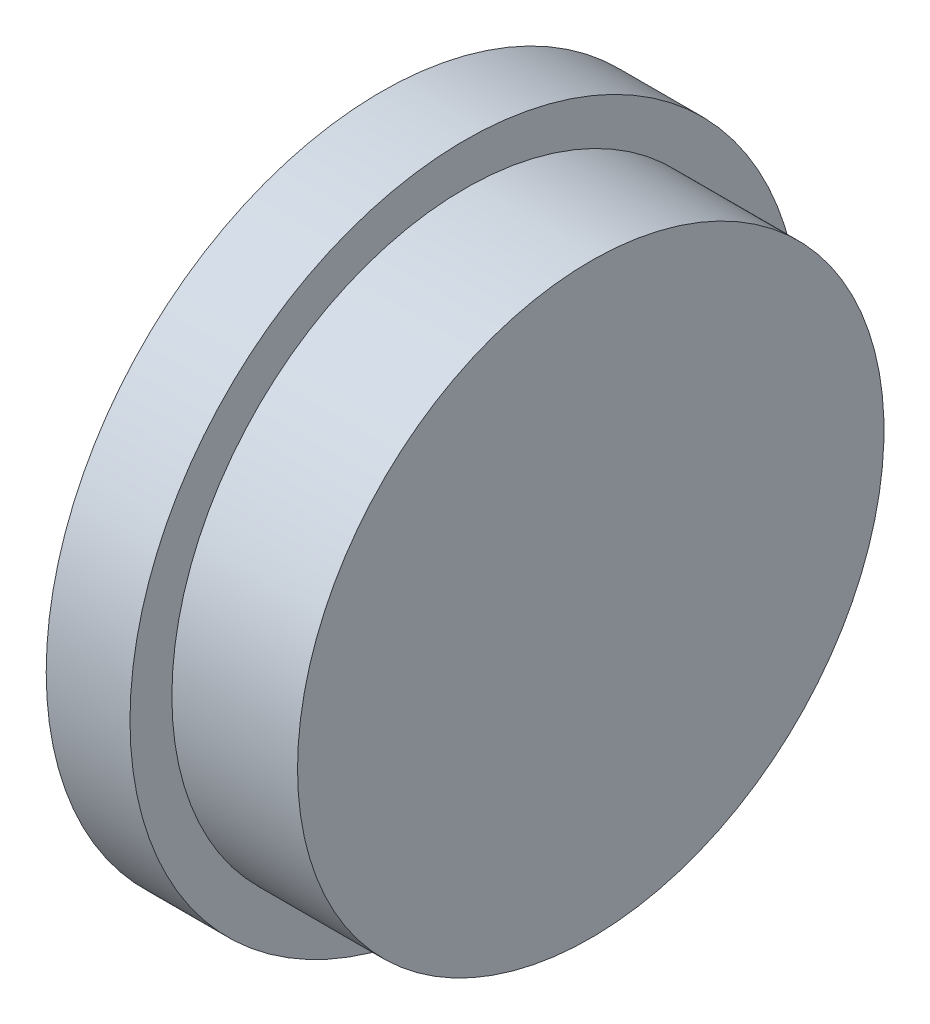
SolidWorks part; units mm, degrees
ref_plane "Plan de face" through (0, 0, 0) normal (0, 0, 1) x (1, 0, 0)
ref_plane "Plan de dessus" through (0, 0, 0) normal (0, 1, 0) x (1, 0, 0)
ref_plane "Plan de droite" through (0, 0, 0) normal (1, 0, 0) x (0, 0, -1)
sketch "Esquisse2" plane through (0, 0, 0) normal (0, 0, 1) x (1, 0, 0)
  line L0 (0, 0) -> (13, 0) construction
  line L1 (13, 0) -> (13, 16)
  line L2 (13, 16) -> (0, 16)
  line L3 (0, 16) -> (0, 24)
  line L4 (0, 24) -> (6, 24)
  line L5 (6, 24) -> (6, 21)
  line L6 (6, 21) -> (15, 21)
  line L7 (15, 21) -> (15, 0)
  line L8 (15, 0) -> (13, 0)
  line L9 (0, 16) -> (0, 0) construction
  dimension "D1" = 15
  dimension "D2" = 21
  dimension "D3" = 8
  dimension "D4" = 16
  dimension "D5" = 6
  dimension "D6" = 2
revolve "Révolution1" add sketch "Esquisse2" angle 360 about L0
